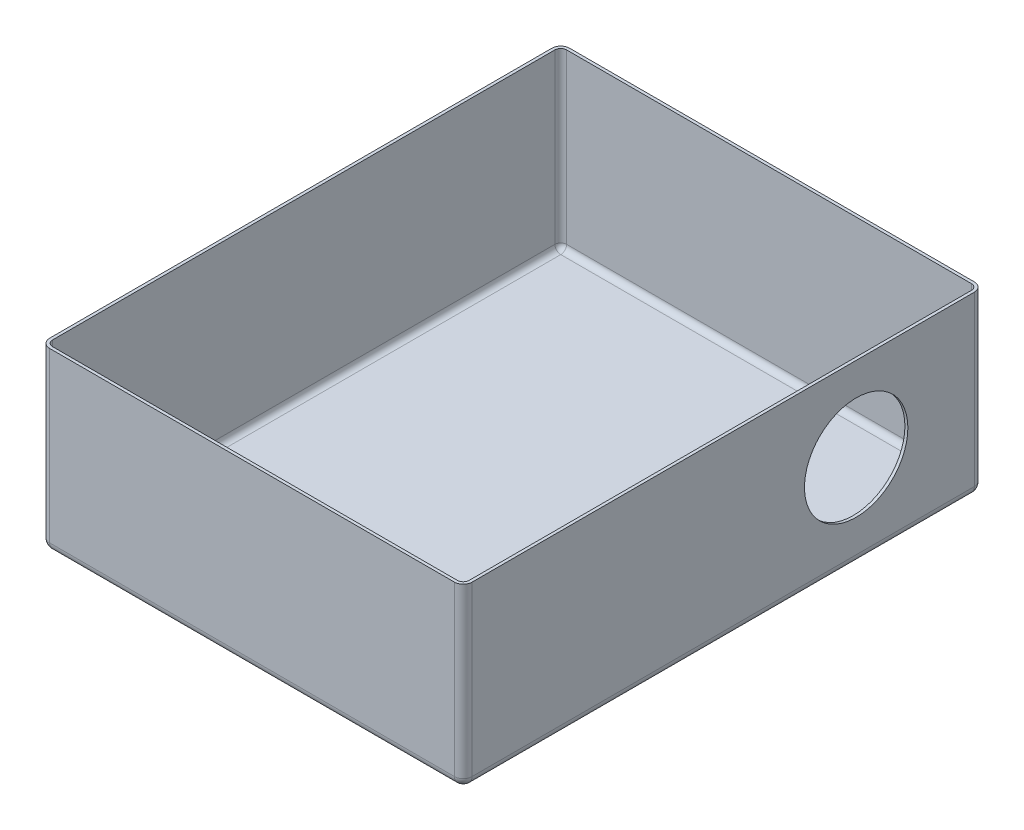
SolidWorks part; units mm, degrees
ref_plane "Front Plane" through (0, 0, 0) normal (0, 0, 1) x (1, 0, 0)
ref_plane "Top Plane" through (0, 0, 0) normal (0, 1, 0) x (1, 0, 0)
ref_plane "Right Plane" through (0, 0, 0) normal (1, 0, 0) x (0, 0, -1)
sketch "Sketch1" plane through (0, 0, 0) normal (0, 1, 0) x (1, 0, 0)
  line L1 (-71.5, -88) -> (71.5, -88)
  line L2 (-71.5, -88) -> (-71.5, 88)
  line L3 (-71.5, 88) -> (71.5, 88)
  line L4 (71.5, -88) -> (71.5, 88)
  line L5 (-71.5, -88) -> (71.5, 88) construction
  line L6 (-71.5, 88) -> (71.5, -88) construction
  point P0 (0, 0)
  dimension "D1" = 143
  dimension "D2" = 176
extrude "Boss-Extrude1" add sketch "Sketch1" along normal blind 60
fillet "Fillet1" radius 3 4 edges at (-71.5, 30, 88) (71.5, 30, 88) (71.5, 30, -88) (-71.5, 30, -88)
fillet "Fillet2" radius 3 8 edges at (70.6213, 0, 87.1213) (71.5, 0, 0) (70.6213, 0, -87.1213) (0, 0, -88) (-70.6213, 0, -87.1213) (-71.5, 0, 0) (-70.6213, 0, 87.1213) (0, 0, 88)
shell "Shell1" thickness 1
sketch "Sketch2" plane through (71.5, 0, 0) normal (1, 0, 0) x (0, 0, -1)
  line L0 (94.4445, 31.5) -> (-131.7458, 31.5) construction
  line L1 (85, 3) -> (85, 60) construction
  line L2 (-85, 60) -> (85, 60) construction
  line L3 (-85, 3) -> (85, 3) construction
  circle A0 centre (45, 31.5) radius 17.5
  point P6 (45, 32.1939)
  dimension "D1" = 35
  dimension "D2" = 40
extrude "Cut-Extrude1" cut sketch "Sketch2" against normal blind 60
